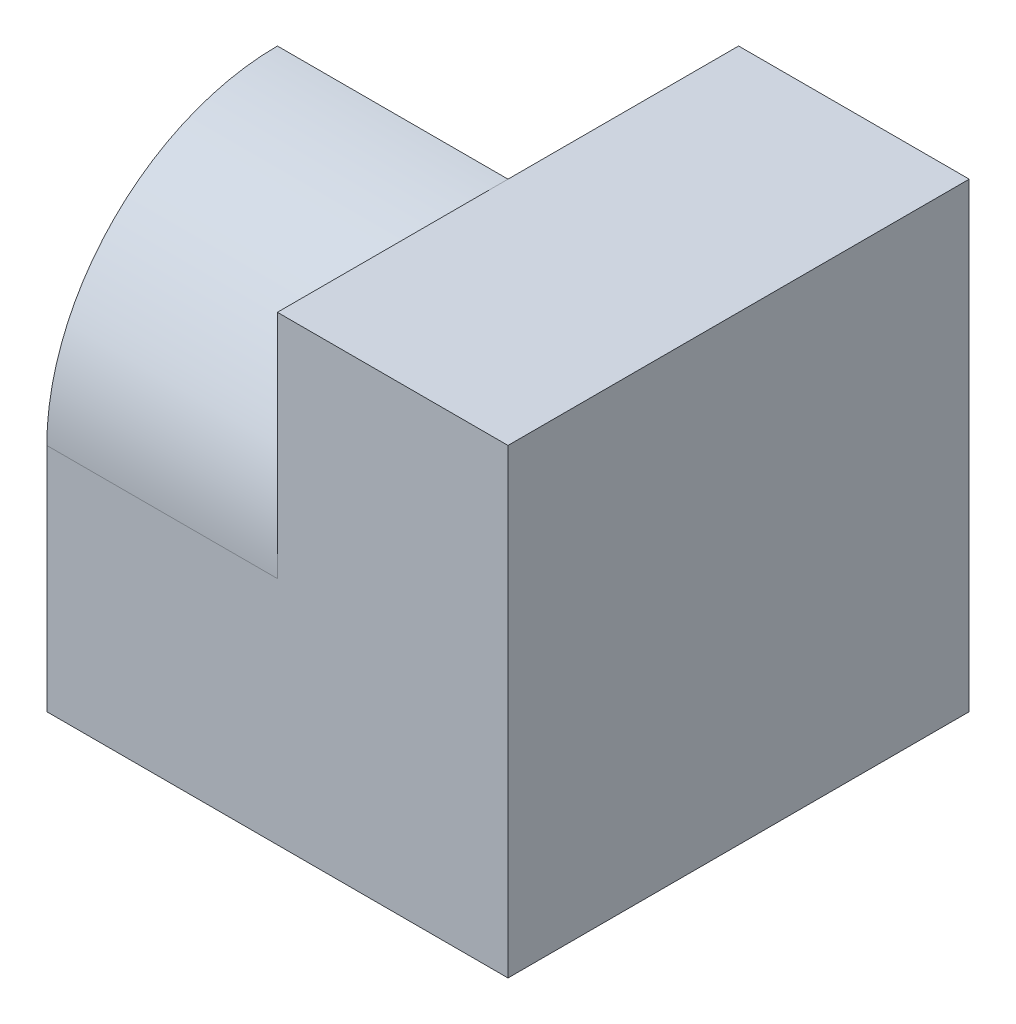
SolidWorks part; units mm, degrees
ref_plane "Front" through (0, 0, 0) normal (0, 0, 1) x (1, 0, 0)
ref_plane "Top" through (0, 0, 0) normal (0, 1, 0) x (1, 0, 0)
ref_plane "Right" through (0, 0, 0) normal (1, 0, 0) x (0, 0, -1)
sketch "Sketch1" plane through (0, 0, 0) normal (0, 1, 0) x (1, 0, 0)
  line L1 (-2, -2) -> (2, -2)
  line L2 (-2, -2) -> (-2, 2)
  line L3 (-2, 2) -> (2, 2)
  line L4 (2, -2) -> (2, 2)
  line L5 (-2, -2) -> (2, 2) construction
  line L6 (-2, 2) -> (2, -2) construction
  point P0 (0, 0)
  dimension "D1" = 4
  dimension "D2" = 4
extrude "Boss-Extrude1" add sketch "Sketch1" along normal blind 4
sketch "Sketch2" plane through (-2, 0, 0) normal (-1, 0, 0) x (0, 0, 1)
  line L2 (-2, 4) -> (2, 4) construction
  line L3 (0, 4) -> (-2, 2)
  line L4 (-2, 4) -> (-2, 0) construction
  line L9 (-2, 0) -> (2, 0)
  line L10 (2, 0) -> (2, 4)
  line L11 (2, 4) -> (-2, 4)
  line L12 (-2, 4) -> (-2, 0)
  line L13 (-2, 0) -> (2, 0)
  line L14 (2, 0) -> (2, 4)
  line L15 (2, 4) -> (-2, 4)
  line L16 (-2, 4) -> (-2, 0)
  arc A0 (0, 4) -> (2, 2) centre (0, 2) cw
  dimension "D1" = 0
extrude "Cut-Extrude1" cut sketch "Sketch2" against normal blind 2
